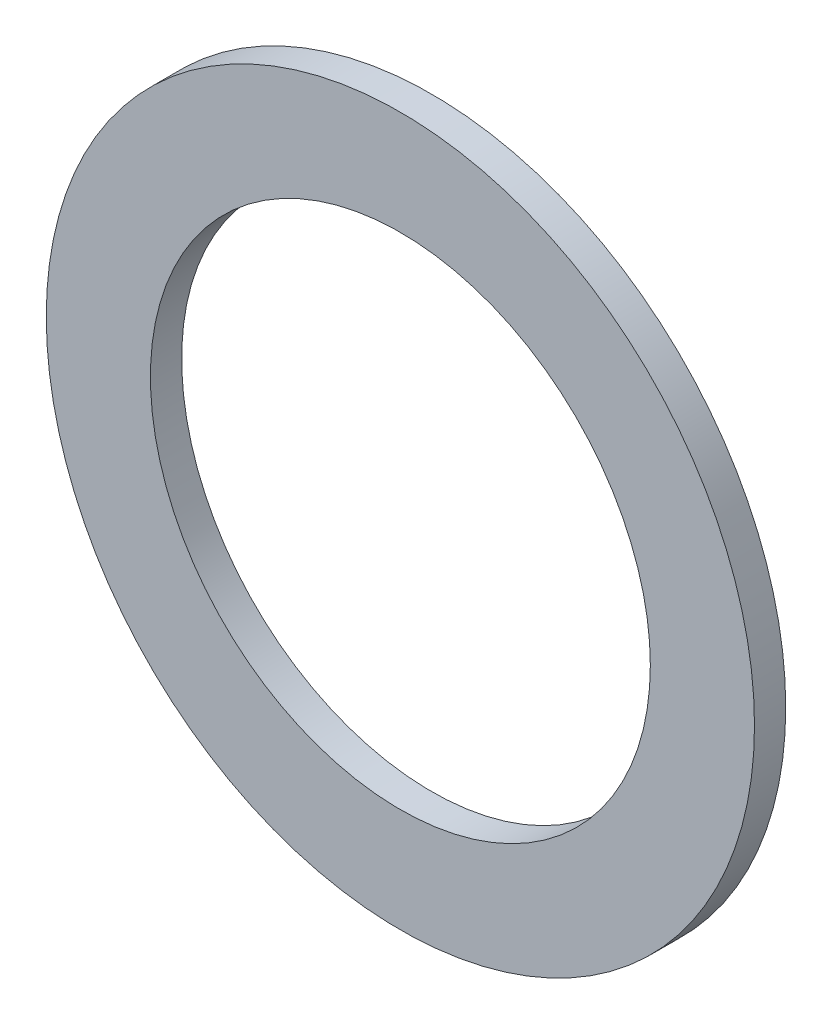
SolidWorks part; units mm, degrees
ref_plane "Спереди" through (0, 0, 0) normal (0, 0, 1) x (1, 0, 0)
ref_plane "Сверху" through (0, 0, 0) normal (0, 1, 0) x (1, 0, 0)
ref_plane "Справа" through (0, 0, 0) normal (1, 0, 0) x (0, 0, -1)
sketch "Эскиз1" plane through (0, 0, 0) normal (0, 0, 1) x (1, 0, 0)
  circle A0 centre (0, 0) radius 12
extrude "Вытянуть-Тонкостенный1" add sketch "Эскиз1" along normal blind 1.5 thin
